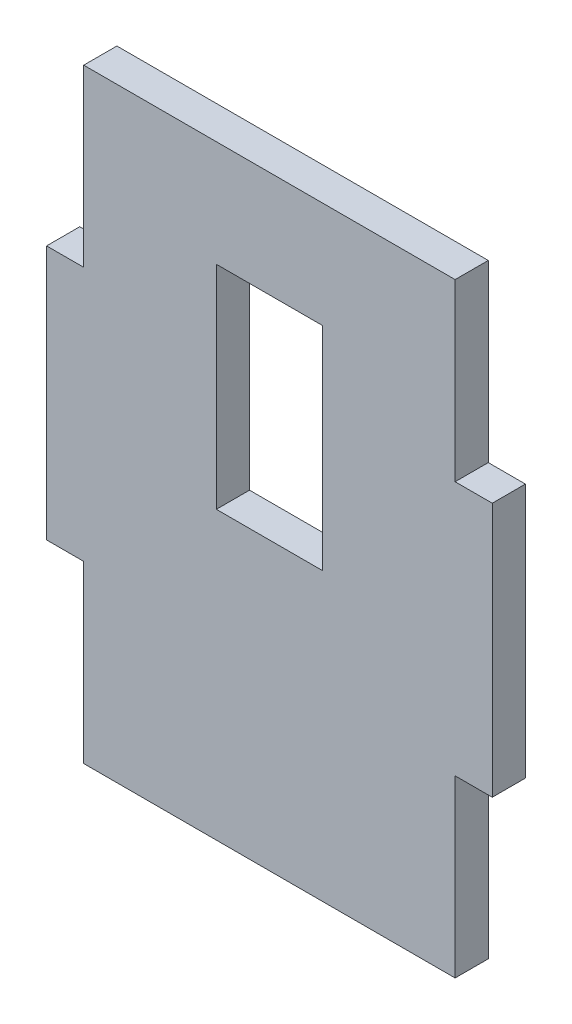
SolidWorks part; units mm, degrees
ref_plane "Front Plane" through (0, 0, 0) normal (0, 0, 1) x (1, 0, 0)
ref_plane "Top Plane" through (0, 0, 0) normal (0, 1, 0) x (1, 0, 0)
ref_plane "Right Plane" through (0, 0, 0) normal (1, 0, 0) x (0, 0, -1)
sketch "Sketch1" plane through (0, 0, 0) normal (0, 0, 1) x (1, 0, 0)
  line L0 (-109.7793, 16.1172) -> (226.2207, 16.1172) construction
  line L1 (-109.7793, 244.1172) -> (226.2207, 244.1172)
  line L2 (-109.7793, 244.1172) -> (-109.7793, -211.8828)
  line L3 (-109.7793, -211.8828) -> (226.2207, -211.8828)
  line L4 (226.2207, 244.1172) -> (226.2207, -211.8828)
  dimension "D1" = 456
  dimension "D2" = 336
extrude "Boss-Extrude1" add sketch "Sketch1" along normal blind 25
sketch "Sketch3" plane through (0, 0, 0) normal (0, 0, 1) x (1, 0, 0)
  line L0 (58.2207, 244.1172) -> (58.2207, -211.8828) construction
  line L1 (-109.7793, 244.1172) -> (-81.7793, 244.1172)
  line L2 (-109.7793, 244.1172) -> (-109.7793, 112.1172)
  line L3 (-109.7793, 112.1172) -> (-81.7793, 112.1172)
  line L4 (-81.7793, 244.1172) -> (-81.7793, 112.1172)
  line L5 (226.2207, 244.1172) -> (-109.7793, 244.1172) construction
  line L6 (-109.7793, -211.8828) -> (226.2207, -211.8828) construction
  line L7 (-109.7793, 16.1172) -> (226.2207, 16.1172) construction
  line L8 (-109.7793, 244.1172) -> (-109.7793, -211.8828) construction
  line L9 (226.2207, -211.8828) -> (226.2207, 244.1172) construction
  line L10 (226.2207, 244.1172) -> (198.2207, 244.1172)
  line L11 (226.2207, 244.1172) -> (226.2207, 112.1172)
  line L12 (226.2207, 112.1172) -> (198.2207, 112.1172)
  line L13 (198.2207, 244.1172) -> (198.2207, 112.1172)
  line L14 (226.2207, -211.8828) -> (198.2207, -211.8828)
  line L15 (226.2207, -211.8828) -> (226.2207, -79.8828)
  line L16 (226.2207, -79.8828) -> (198.2207, -79.8828)
  line L17 (198.2207, -211.8828) -> (198.2207, -79.8828)
  line L18 (-109.7793, -79.8828) -> (-81.7793, -79.8828)
  line L19 (-109.7793, -211.8828) -> (-109.7793, -79.8828)
  line L20 (-109.7793, -211.8828) -> (-81.7793, -211.8828)
  line L21 (-81.7793, -211.8828) -> (-81.7793, -79.8828)
  dimension "D1" = 28
  dimension "D2" = 132
extrude "Cut-Extrude1" cut sketch "Sketch3" along normal blind 25
sketch "Sketch4" plane through (0, 0, 25) normal (0, 0, 1) x (1, 0, 0)
  line L0 (198.2207, 244.1172) -> (-81.7793, 244.1172) construction
  line L1 (18.2207, 164.1172) -> (98.2207, 164.1172)
  line L2 (18.2207, 164.1172) -> (18.2207, 4.1172)
  line L3 (18.2207, 4.1172) -> (98.2207, 4.1172)
  line L4 (98.2207, 164.1172) -> (98.2207, 4.1172)
  line L5 (198.2207, 244.1172) -> (198.2207, 112.1172) construction
  dimension "D1" = 80
  dimension "D2" = 160
  dimension "D3" = 80
  dimension "D4" = 100
extrude "Cut-Extrude2" cut sketch "Sketch4" against normal blind 25
